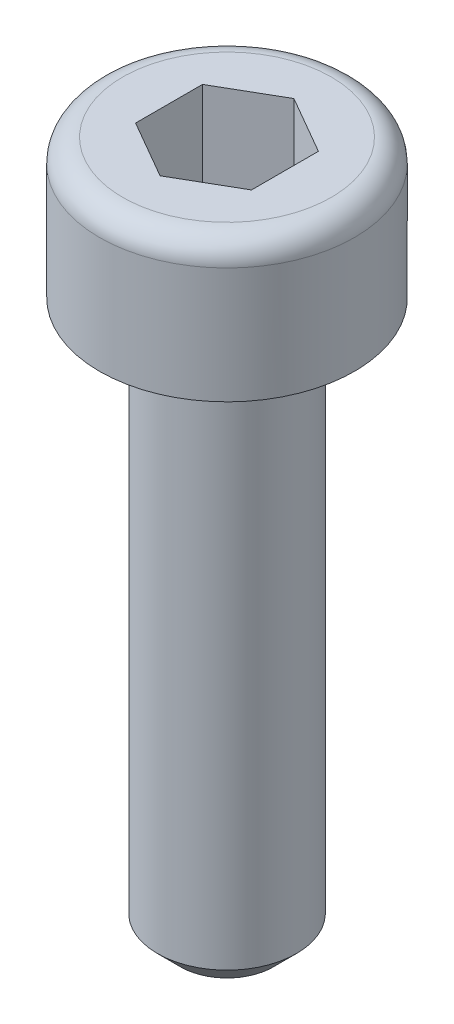
SolidWorks part; units mm, degrees
material "acero"
ref_plane "Alzado" through (0, 0, 0) normal (0, 0, 1) x (1, 0, 0)
ref_plane "Planta" through (0, 0, 0) normal (0, 1, 0) x (1, 0, 0)
ref_plane "Vista lateral" through (0, 0, 0) normal (1, 0, 0) x (0, 0, -1)
sketch "Croquis1" plane through (0, 0, 0) normal (0, 0, 1) x (1, 0, 0)
  line L0 (0, 0) -> (0, -60.9498) construction
  line L1 (0, 0) -> (2.75, 0)
  line L2 (2.75, 0) -> (2.75, -3)
  line L3 (2.75, -3) -> (1.5, -3)
  line L4 (1.5, -3) -> (1.5, -15)
  line L5 (1.5, -15) -> (0, -15)
  line L6 (0, -15) -> (0, 0)
  dimension "D1" = 12
  dimension "D2" = 3
  dimension "D3" = 5.5
  dimension "D4" = 3
revolve "Revolución1" add sketch "Croquis1" angle 360 about L0
sketch "Croquis2" plane through (0, 0, 0) normal (0, 1, 0) x (1, 0, 0)
  line L1 (1.25, 0.7217) -> (0, 1.4434)
  line L2 (0, 1.4434) -> (-1.25, 0.7217)
  line L3 (-1.25, 0.7217) -> (-1.25, -0.7217)
  line L4 (-1.25, -0.7217) -> (0, -1.4434)
  line L5 (0, -1.4434) -> (1.25, -0.7217)
  line L6 (1.25, -0.7217) -> (1.25, 0.7217)
  circle A0 centre (0, 0) radius 1.25 construction
  dimension "D1" = 2.5
extrude "Cortar-Extruir1" cut sketch "Croquis2" against normal blind 2
chamfer "Chaflán1" distance 0.5 angle 45 1 edges at (0, -15, 1.5)
fillet "Redondeo1" radius 0.5 1 edges at (0, 0, 2.75)
